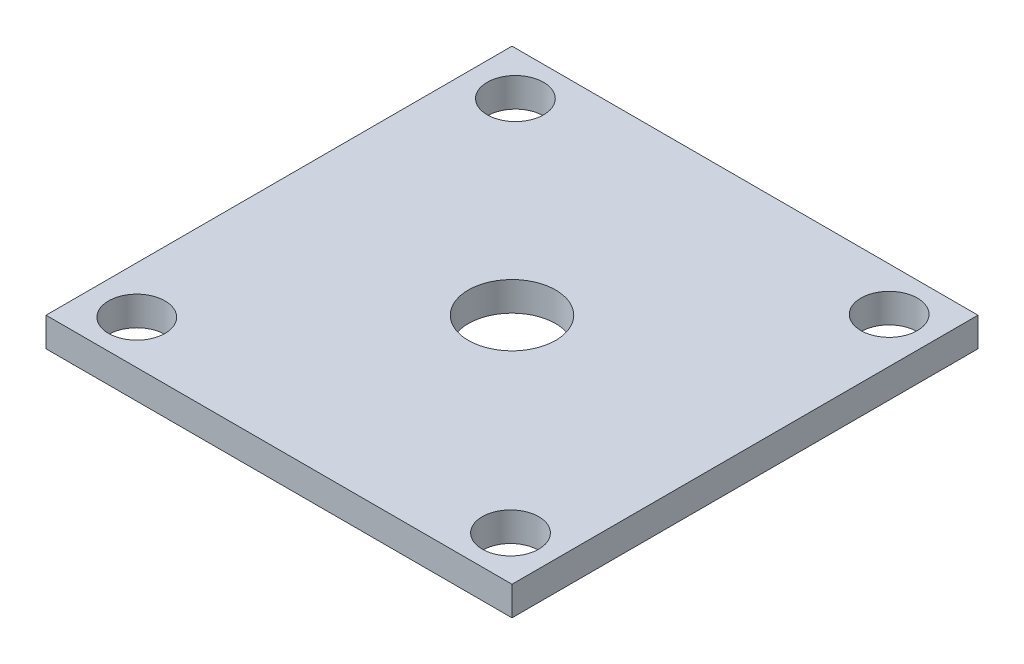
SolidWorks part; units mm, degrees
ref_plane "Front Plane" through (0, 0, 0) normal (0, 0, 1) x (1, 0, 0)
ref_plane "Top Plane" through (0, 0, 0) normal (0, 1, 0) x (1, 0, 0)
ref_plane "Right Plane" through (0, 0, 0) normal (1, 0, 0) x (0, 0, -1)
sketch "Sketch1" plane through (0, 0, 0) normal (0, 1, 0) x (1, 0, 0)
  line L1 (0, 0) -> (101.6, 0)
  line L2 (0, 0) -> (0, 101.6)
  line L3 (0, 101.6) -> (101.6, 101.6)
  line L4 (101.6, 0) -> (101.6, 101.6)
extrude "Boss-Extrude1" add sketch "Sketch1" along normal blind 6.35
hole_wizard "9/16-12 Tapped Hole1" positions "Sketch2" profile "Sketch3" tap size "9/16-12" standard "ANSI Inch" end condition through all
sketch "Sketch2" plane through (0, 6.35, 0) normal (0, 1, 0) x (1, 0, 0)
  line L0 (101.6, 101.6) -> (0, 101.6) construction
  line L1 (0, 0) -> (101.6, 0) construction
  point P0 (10.2661, 92.075)
  point P2 (91.7517, 9.525)
  point P11 (91.7517, 92.075)
  point P13 (10.2661, 9.525)
  dimension "D1" = 9.525
  dimension "D2" = 9.525
sketch "Sketch3" plane through (10.2661, 6.35, -92.075) normal (1, 0, 0) x (0, 0, 1)
  line L0 (0, 0) -> (0, 6.35)
  line L1 (0, 6.35) -> (6.1519, 6.35)
  line L2 (6.1519, 6.35) -> (6.1519, 0)
  line L5 (6.1519, 0) -> (0, 0)
  line L11 (0, -6.35) -> (0, 107.95) construction
  dimension "Thru Tap Drill Dia." = 12.3038
  dimension "Thru Tap Drill Depth" = 6.35
cosmetic thread "Hole Thread1"
cosmetic thread "Hole Thread2"
cosmetic thread "Hole Thread3"
cosmetic thread "Hole Thread4"
hole_wizard "3/4 (0.75) Diameter Hole1" positions "Sketch8" profile "Sketch7" hole size "3/4" standard "ANSI Inch" end condition through all
sketch "Sketch8" plane through (0, 6.35, 0) normal (0, 1, 0) x (1, 0, 0)
  line L0 (50.8, 101.6) -> (50.8, 0) construction
  line L1 (101.6, 101.6) -> (0, 101.6) construction
  line L2 (0, 0) -> (101.6, 0) construction
  line L4 (0, 50.8) -> (101.6, 50.8) construction
  line L5 (0, 101.6) -> (0, 0) construction
  line L6 (101.6, 0) -> (101.6, 101.6) construction
  point P0 (50.8, 50.8)
  point P19 (0, 0)
  point P21 (50.8, 50.8)
  dimension "D1" = 0
sketch "Sketch7" plane through (50.8, 6.35, -50.8) normal (1, 0, 0) x (0, 0, 1)
  line L0 (0, 0) -> (0, 6.35)
  line L1 (0, 6.35) -> (9.525, 6.35)
  line L2 (9.525, 6.35) -> (9.525, 0)
  line L5 (9.525, 0) -> (0, 0)
  line L11 (0, -6.35) -> (0, 107.95) construction
  dimension "Thru Hole Dia." = 19.05
  dimension "Thru Hole Depth" = 6.35
